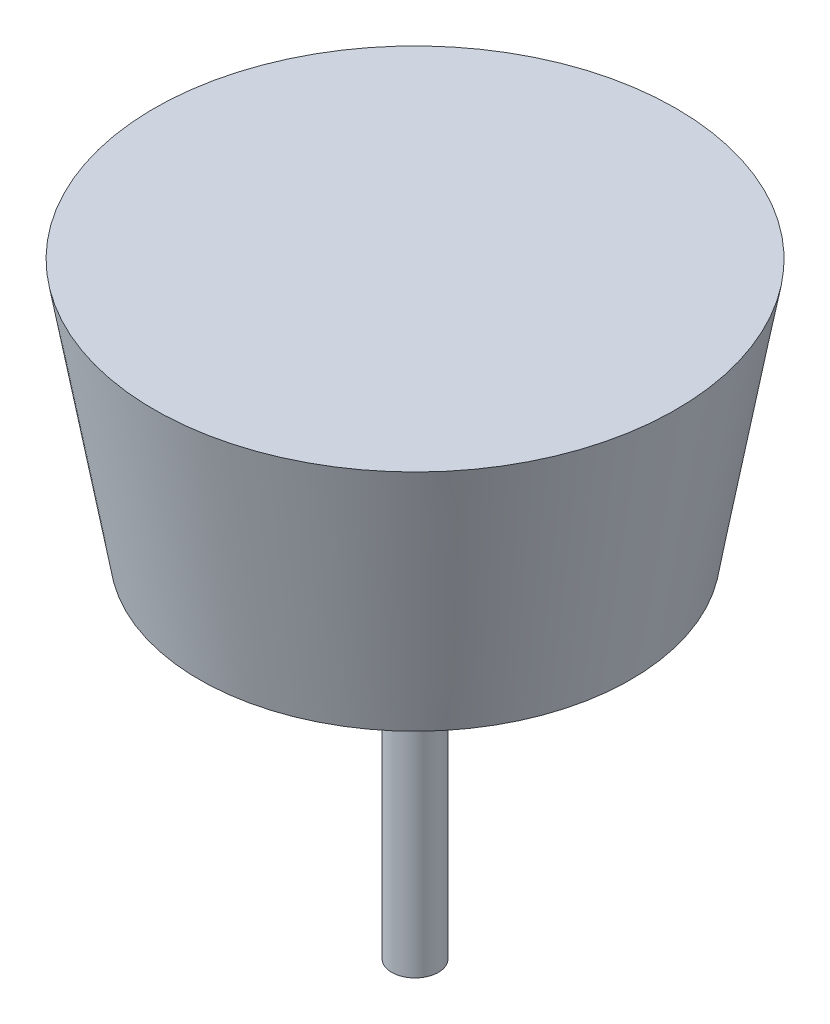
SolidWorks part; units mm, degrees
other "Camera4"
other "Camera5"
ref_plane "Front Plane" through (0, 0, 0) normal (0, 0, 1) x (1, 0, 0)
ref_plane "Top Plane" through (0, 0, 0) normal (0, 1, 0) x (1, 0, 0)
ref_plane "Right Plane" through (0, 0, 0) normal (1, 0, 0) x (0, 0, -1)
sketch "Sketch1" plane through (0, 0, 0) normal (0, 0, 1) x (1, 0, 0)
  line L0 (0, 0) -> (0, 25)
  line L1 (0, 25) -> (1, 25)
  line L2 (1, 25) -> (1, 0)
  line L4 (1, 0) -> (0, 0)
  line L5 (0, 0) -> (0, 29.3148) construction
  dimension "D1" = 25
  dimension "D2" = 1
revolve "Revolve1" add sketch "Sketch1" angle 360 about L0
sketch "Sketch2" plane through (0, 0, 0) normal (0, 0, 1) x (1, 0, 0)
  line L0 (0, 25) -> (10, 25)
  line L1 (10, 25) -> (8.2673, 15.1736)
  line L2 (8.2673, 15.1736) -> (9.2522, 15)
  line L3 (9.2522, 15) -> (11.1918, 26)
  line L4 (11.1918, 26) -> (0, 26)
  line L5 (0, -200000) -> (0, 200029.3148) construction
  line L6 (0, 26) -> (0, 25)
  dimension "D1" = 1
  dimension "D2" = 10
  dimension "D3" = 1
  dimension "D4" = 10
  dimension "D5" = 80
revolve "Revolve2" add sketch "Sketch2" angle 360 about L0
